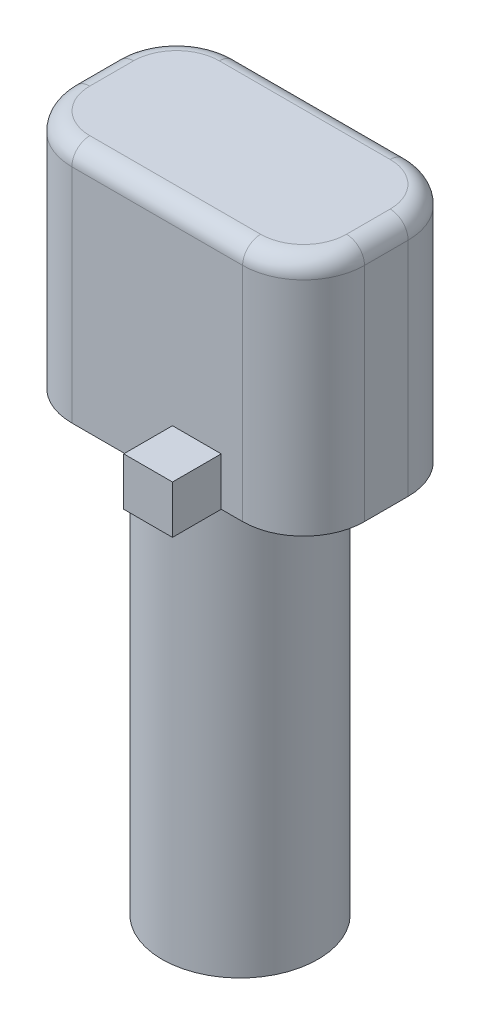
SolidWorks part; units mm, degrees
ref_plane "Front Plane" through (0, 0, 0) normal (0, 0, 1) x (1, 0, 0)
ref_plane "Top Plane" through (0, 0, 0) normal (0, 1, 0) x (1, 0, 0)
ref_plane "Right Plane" through (0, 0, 0) normal (1, 0, 0) x (0, 0, -1)
sketch "Sketch1" plane through (0, 0, 0) normal (0, 1, 0) x (1, 0, 0)
  circle A0 centre (0, 0) radius 3.25
  dimension "D1" = 6.5
extrude "Boss-Extrude1" add sketch "Sketch1" along normal blind 17.686 contours A0
sketch "Sketch2" plane through (0, 0, 0) normal (0, -1, 0) x (1, 0, 0)
  circle A1 centre (0, 0) radius 1.75
  dimension "D1" = 3.5
extrude "Cut-Extrude1" [suppressed] cut sketch "Sketch2" against normal blind 2.5
sketch "Sketch3" plane through (0, 17.686, 0) normal (0, 1, 0) x (1, 0, 0)
  line L1 (-6.1, 3.45) -> (6.1, 3.45)
  line L2 (-6.1, 3.45) -> (-6.1, -3.45)
  line L3 (-6.1, -3.45) -> (6.1, -3.45)
  line L4 (6.1, 3.45) -> (6.1, -3.45)
  line L5 (-6.1, 3.45) -> (6.1, -3.45) construction
  line L6 (-6.1, -3.45) -> (6.1, 3.45) construction
  point P0 (0, 0)
  dimension "D1" = 12.2
  dimension "D2" = 6.9
extrude "Boss-Extrude2" add sketch "Sketch3" along normal blind 10
fillet "Fillet1" radius 2.54 4 edges at (-6.1, 22.686, -3.45) (6.1, 22.686, -3.45) (6.1, 22.686, 3.45) (-6.1, 22.686, 3.45)
fillet "Fillet2" radius 0.75 8 edges at (6.1, 27.686, 0) (5.3561, 27.686, 2.7061) (5.3561, 27.686, -2.7061) (0, 27.686, -3.45) (-5.3561, 27.686, -2.7061) (-6.1, 27.686, 0) (-5.3561, 27.686, 2.7061) (0, 27.686, 3.45)
sketch "Sketch5" plane through (0, 17.686, 0) normal (0, -1, 0) x (1, 0, 0)
  line L0 (-6.1, 0) -> (6.1, 0) construction
  line L1 (-6.1, -0.91) -> (-6.1, 0.91) construction
  line L2 (6.1, 0.91) -> (6.1, -0.91) construction
  line L6 (0, 3.45) -> (0, -3.45) construction
  line L8 (-3.56, 3.45) -> (3.56, 3.45) construction
  line L9 (3.56, -3.45) -> (-3.56, -3.45) construction
  line L18 (-3.302, -3.45) -> (-1.27, -3.45)
  line L19 (-3.302, -5.482) -> (-3.302, -3.45)
  line L20 (-1.27, -5.482) -> (-3.302, -5.482)
  line L21 (-1.27, -3.45) -> (-1.27, -5.482)
  line L22 (2.667, 3.45) -> (0.635, 3.45)
  line L23 (0.635, 5.482) -> (0.635, 3.45)
  line L24 (2.667, 5.482) -> (0.635, 5.482)
  line L25 (2.667, 3.45) -> (2.667, 5.482)
extrude "Boss-Extrude3" add sketch "Sketch5" against normal blind 2
